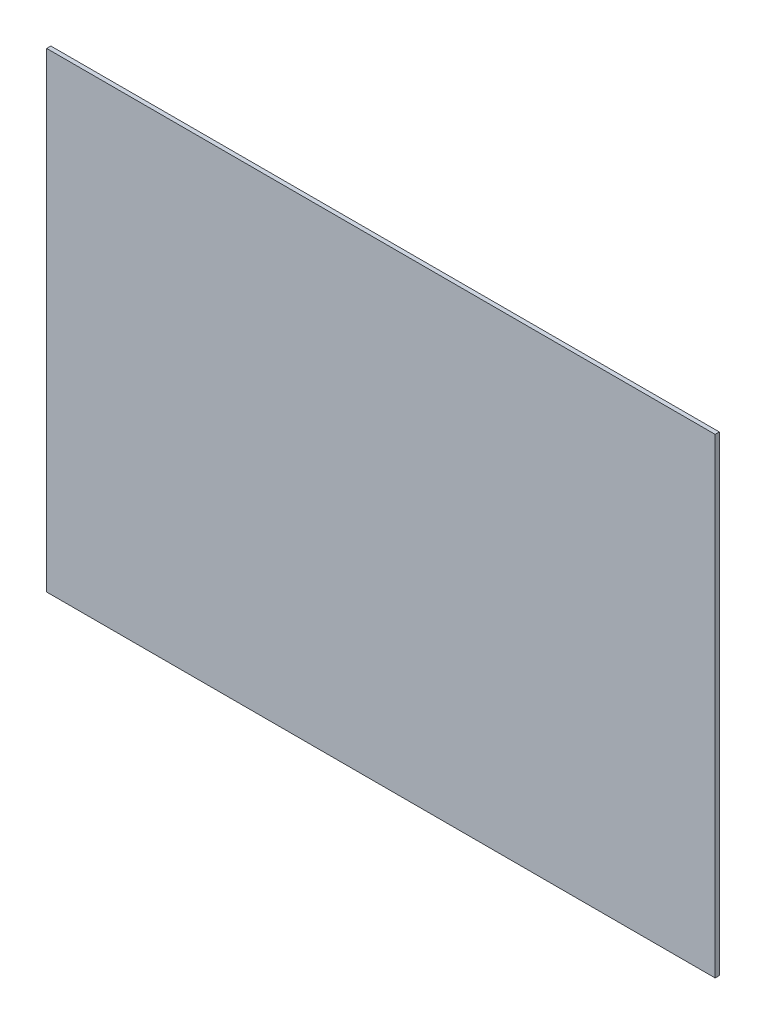
SolidWorks part; units mm, degrees
ref_plane "Front Plane" through (0, 0, 0) normal (0, 0, 1) x (1, 0, 0)
ref_plane "Top Plane" through (0, 0, 0) normal (0, 1, 0) x (1, 0, 0)
ref_plane "Right Plane" through (0, 0, 0) normal (1, 0, 0) x (0, 0, -1)
sketch "Sketch1" plane through (0, 0, 0) normal (0, 0, 1) x (1, 0, 0)
  line L0 (-2.0262, -1.427) -> (2.0262, -1.427)
  line L1 (2.0262, -1.427) -> (2.0262, 1.427)
  line L2 (2.0262, 1.427) -> (-2.0262, 1.427)
  line L3 (-2.0262, 1.427) -> (-2.0262, -1.427)
extrude "Boss-Extrude1" add sketch "Sketch1" along normal blind 0.0254 from offset 0
